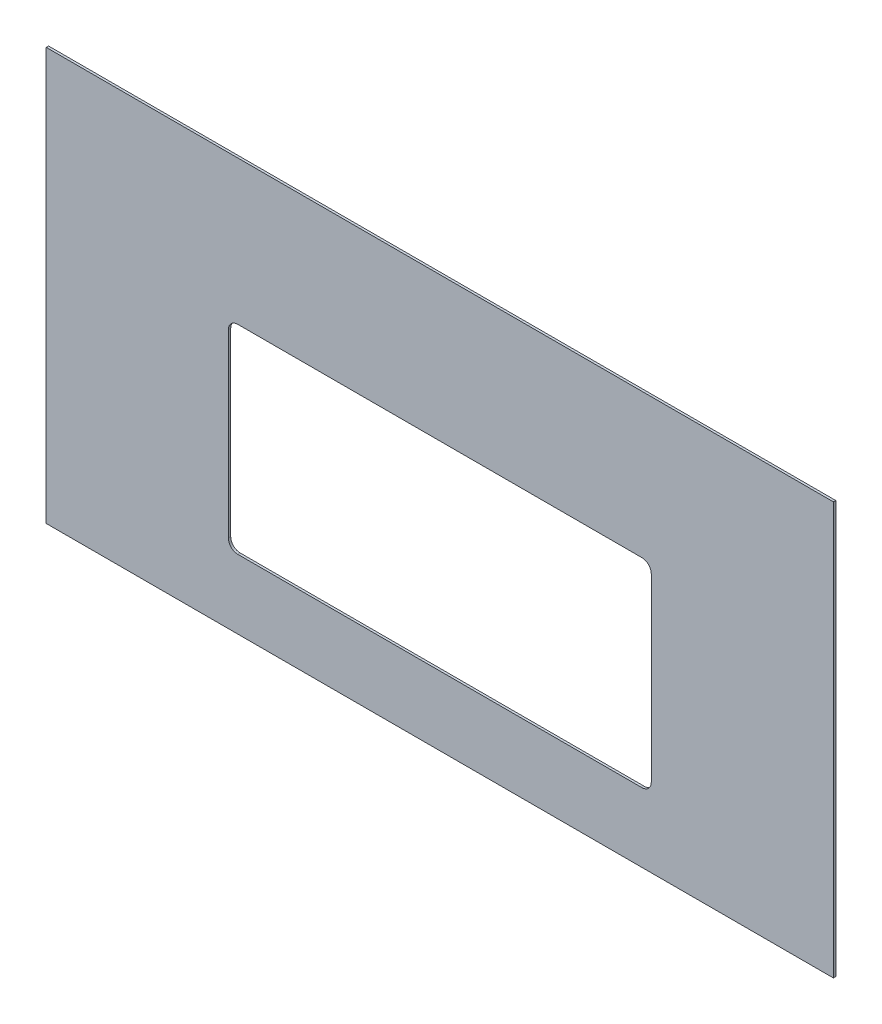
SolidWorks part; units mm, degrees
ref_plane "Front Plane" through (0, 0, 0) normal (0, 0, 1) x (1, 0, 0)
ref_plane "Top Plane" through (0, 0, 0) normal (0, 1, 0) x (1, 0, 0)
ref_plane "Right Plane" through (0, 0, 0) normal (1, 0, 0) x (0, 0, -1)
sketch "Sketch1" plane through (0, 0, 0) normal (0, 0, 1) x (1, 0, 0)
  line L1 (-533.4, 279.4) -> (533.4, 279.4)
  line L2 (-533.4, 279.4) -> (-533.4, -279.4)
  line L3 (-533.4, -279.4) -> (533.4, -279.4)
  line L4 (533.4, 279.4) -> (533.4, -279.4)
  line L5 (-533.4, 279.4) -> (533.4, -279.4) construction
  line L6 (-533.4, -279.4) -> (533.4, 279.4) construction
  point P0 (0, 0)
  dimension "D1" = 1066.8
  dimension "D2" = 558.8
extrude "Boss-Extrude1" add sketch "Sketch1" along normal blind 3.175
sketch "Sketch2" plane through (0, 0, 3.175) normal (0, 0, 1) x (1, 0, 0)
  line L0 (0, -50.8) -> (0, 279.4) construction
  line L1 (-273.8438, 84.1375) -> (273.8437, 84.1375)
  line L2 (-286.5438, 71.4375) -> (-286.5438, -173.0375)
  line L3 (-273.8438, -185.7375) -> (273.8437, -185.7375)
  line L4 (286.5437, 71.4375) -> (286.5437, -173.0375)
  line L5 (-286.5438, 84.1375) -> (286.5437, -185.7375) construction
  line L6 (-286.5438, -185.7375) -> (286.5437, 84.1375) construction
  line L7 (533.4, 279.4) -> (-533.4, 279.4) construction
  line L8 (-533.4, -279.4) -> (533.4, -279.4) construction
  arc A0 (273.8437, 84.1375) -> (286.5437, 71.4375) centre (273.8437, 71.4375) cw
  arc A1 (273.8437, -185.7375) -> (286.5437, -173.0375) centre (273.8437, -173.0375) ccw
  arc A2 (-286.5438, -173.0375) -> (-273.8438, -185.7375) centre (-273.8438, -173.0375) ccw
  arc A3 (-273.8438, 84.1375) -> (-286.5438, 71.4375) centre (-273.8438, 71.4375) ccw
  point P0 (0, -50.8)
  dimension "D4" = 12.7
  dimension "D1" = 269.875
  dimension "D2" = 573.0875
  dimension "D3" = 228.6
extrude "Cut-Extrude1" cut sketch "Sketch2" against normal up to next
